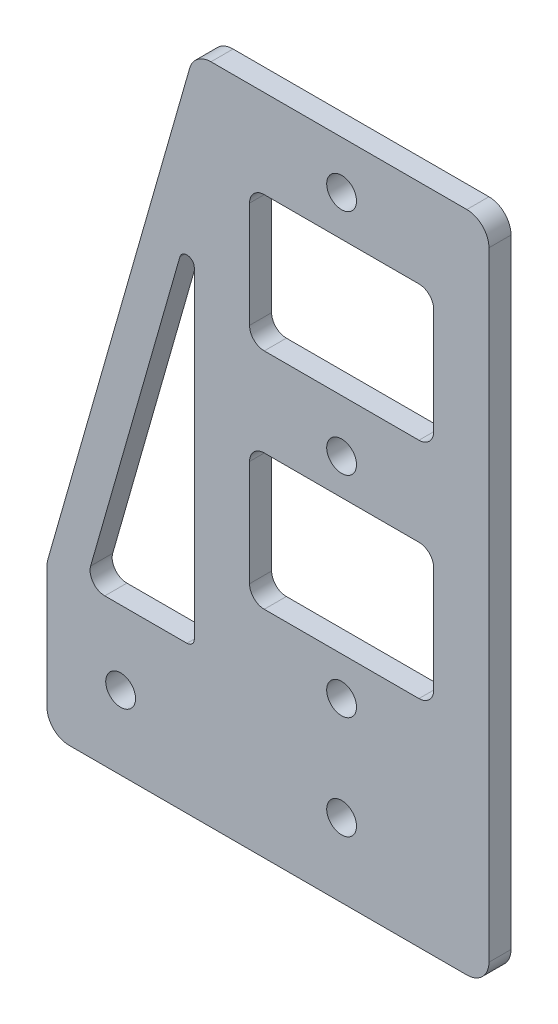
SolidWorks part; units mm, degrees
material "Thornel Mat VMA"
ref_plane "前视基准面" through (0, 0, 0) normal (0, 0, 1) x (1, 0, 0)
ref_plane "上视基准面" through (0, 0, 0) normal (0, 1, 0) x (1, 0, 0)
ref_plane "右视基准面" through (0, 0, 0) normal (1, 0, 0) x (0, 0, -1)
other "Configuration Table"
sketch "草图1" plane through (0, 0, 0) normal (0, 0, 1) x (1, 0, 0)
  line L0 (0, 0) -> (-60, 0)
  line L1 (-60, 0) -> (-60, 20)
  line L2 (-60, 20) -> (-40, 90)
  line L3 (-40, 90) -> (0, 90)
  line L4 (0, 90) -> (0, 0)
  dimension "D1" = 40
  dimension "D2" = 20
  dimension "D3" = 60
  dimension "D4" = 90
extrude "凸台-拉伸1" add sketch "草图1" along normal mid plane 3
sketch "草图2" plane through (0, 0, 1.5) normal (0, 0, 1) x (1, 0, 0)
  line L0 (-40, 71.7997) -> (-54.7999, 20)
  line L1 (-54.7999, 20) -> (-40, 20)
  line L2 (-40, 20) -> (-40, 71.7997)
  line L3 (-40, 90) -> (-60, 20) construction
  line L4 (0, 0) -> (0, 90) construction
  dimension "D1" = 5
  dimension "D2" = 40
extrude "切除-拉伸1" cut sketch "草图2" against normal through all
fillet "圆角1" radius 1 2 edges at (-40, 20, 0) (-40, 71.7997, 0)
sketch "草图3" plane through (0, 0, 1.5) normal (0, 0, 1) x (1, 0, 0)
  line L0 (-54.7999, 20) -> (-41, 20) construction
  line L1 (-32.5, 59.625) -> (-7.5, 59.625)
  line L2 (-32.5, 59.625) -> (-32.5, 78)
  line L3 (-32.5, 78) -> (-7.5, 78)
  line L4 (-7.5, 59.625) -> (-7.5, 78)
  line L5 (-32.5, 59.625) -> (-7.5, 78) construction
  line L6 (-32.5, 78) -> (-7.5, 59.625) construction
  line L7 (-32.5, 29.25) -> (-7.5, 29.25)
  line L8 (-32.5, 29.25) -> (-32.5, 47.625)
  line L9 (-32.5, 47.625) -> (-7.5, 47.625)
  line L10 (-7.5, 29.25) -> (-7.5, 47.625)
  line L11 (-32.5, 29.25) -> (-7.5, 47.625) construction
  line L12 (-32.5, 47.625) -> (-7.5, 29.25) construction
  line L14 (0, 90) -> (-40, 90) construction
  line L15 (-40, 42.8298) -> (0, 42.8298) construction
  line L16 (-40, 21) -> (-40, 64.6597) construction
  line L17 (0, 0) -> (0, 90) construction
  point P0 (-20, 68.8125)
  point P5 (-20, 38.4375)
  point P20 (-20, 42.8298)
  dimension "D1" = 9.25
  dimension "D2" = 25
  dimension "D4" = 12
  dimension "D5" = 12
extrude "切除-拉伸2" cut sketch "草图3" against normal through all
fillet "圆角2" radius 2 8 edges at (-7.5, 59.625, 0) (-32.5, 78, 0) (-7.5, 78, 0) (-32.5, 59.625, 0) (-7.5, 29.25, 0) (-32.5, 29.25, 0) (-32.5, 47.625, 0) (-7.5, 47.625, 0)
sketch "草图4" plane through (0, 0, 1.5) normal (0, 0, 1) x (1, 0, 0)
  line L0 (-60, 0) -> (0, 0) construction
  line L1 (0, 90) -> (-40, 90) construction
  line L2 (-20, 90) -> (-20, 0) construction
  circle A0 centre (-50, 10) radius 2.025
  circle A1 centre (-20, 10) radius 2.025
  circle A2 centre (-20, 24) radius 2.025
  circle A3 centre (-20, 52.5) radius 2.025
  circle A4 centre (-20, 83.5) radius 2.025
  dimension "D1" = 4.05
  dimension "D2" = 30
  dimension "D3" = 10
  dimension "D4" = 14
  dimension "D5" = 28.5
  dimension "D6" = 31
extrude "切除-拉伸3" cut sketch "草图4" against normal blind 10
fillet "圆角3" radius 3 5 edges at (0, 0, 0) (-60, 0, 0) (-60, 20, 0) (0, 90, 0) (-40, 90, 0)
fillet "圆角4" radius 2 1 edges at (-54.7999, 20, 0)
